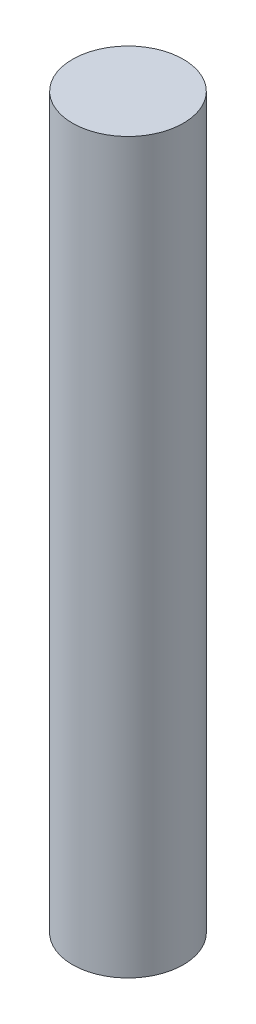
SolidWorks part; units mm, degrees
ref_plane "Front Plane" through (0, 0, 0) normal (0, 0, 1) x (1, 0, 0)
ref_plane "Top Plane" through (0, 0, 0) normal (0, 1, 0) x (1, 0, 0)
ref_plane "Right Plane" through (0, 0, 0) normal (1, 0, 0) x (0, 0, -1)
sketch "Sketch2" plane through (0, 0, 0) normal (0, 1, 0) x (1, 0, 0)
  circle A0 centre (0, 0) radius 1.825
  dimension "D1" = 3.65
extrude "Boss-Extrude1" add sketch "Sketch2" along normal blind 24
